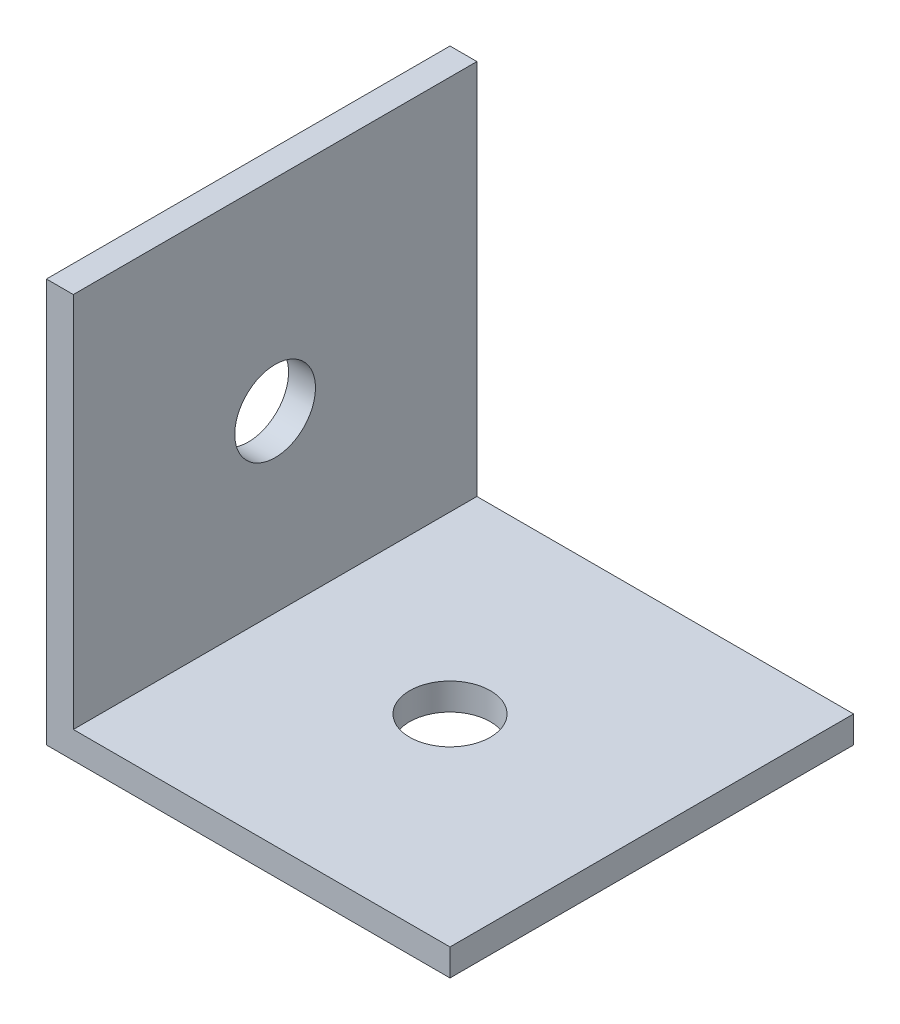
SolidWorks part; units mm, degrees
material "1060 合金"
ref_plane "正面" through (0, 0, 0) normal (0, 0, 1) x (1, 0, 0)
ref_plane "平面" through (0, 0, 0) normal (0, 1, 0) x (1, 0, 0)
ref_plane "右側面" through (0, 0, 0) normal (1, 0, 0) x (0, 0, -1)
sketch "ｽｹｯﾁ1" plane through (0, 0, 0) normal (0, 0, 1) x (1, 0, 0)
  line L1 (-5.4615, 6.3533) -> (9.5385, 6.3533)
  line L2 (-5.4615, 6.3533) -> (-5.4615, -8.6467)
  line L3 (-5.4615, -8.6467) -> (9.5385, -8.6467)
  line L4 (9.5385, 6.3533) -> (9.5385, -8.6467)
  line L5 (9.5385, 6.3533) -> (-4.4615, 6.3533)
  line L6 (9.5385, 6.3533) -> (9.5385, -7.6467)
  line L7 (9.5385, -7.6467) -> (-4.4615, -7.6467)
  line L8 (-4.4615, 6.3533) -> (-4.4615, -7.6467)
  dimension "D1" = 15
  dimension "D2" = 15
  dimension "D3" = 1
  dimension "D4" = 1
extrude "ﾎﾞｽ - 押し出し1" add sketch "ｽｹｯﾁ1" along normal blind 15 contours L8 L1 L2 L3 L4 L7
sketch "ｽｹｯﾁ2" plane through (-5.4615, 0, 0) normal (-1, 0, 0) x (0, 0, 1)
  line L0 (15, 6.3533) -> (0, 6.3533) construction
  circle A0 centre (7.5, -1.1467) radius 1.5
  dimension "D1" = 7.5
extrude "ｶｯﾄ - 押し出し1" cut sketch "ｽｹｯﾁ2" against normal blind 10
sketch "ｽｹｯﾁ3" plane through (0, -8.6467, 0) normal (0, -1, 0) x (1, 0, 0)
  line L0 (-5.4615, 15) -> (-5.4615, 0) construction
  circle A0 centre (2.0385, 7.5) radius 1.5
  dimension "D1" = 7.5
extrude "ｶｯﾄ - 押し出し2" cut sketch "ｽｹｯﾁ3" against normal blind 10
